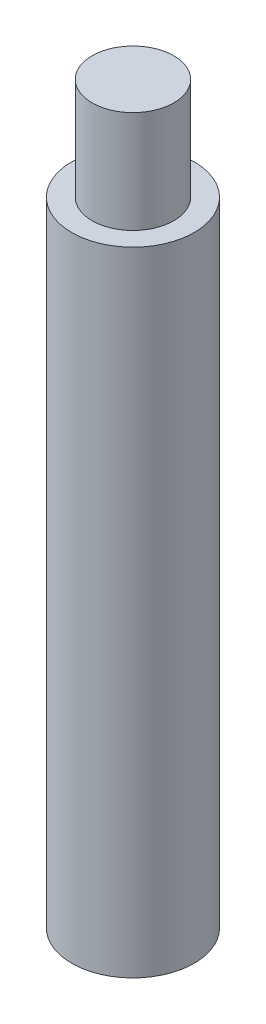
SolidWorks part; units mm, degrees
material "Plain Carbon Steel"
ref_plane "Front Plane" through (0, 0, 0) normal (0, 0, 1) x (1, 0, 0)
ref_plane "Top Plane" through (0, 0, 0) normal (0, 1, 0) x (1, 0, 0)
ref_plane "Right Plane" through (0, 0, 0) normal (1, 0, 0) x (0, 0, -1)
sketch "Sketch1" plane through (0, 0, 0) normal (0, 0, 1) x (1, 0, 0)
  line L0 (0, 0) -> (1.5, 0)
  line L1 (1.5, 0) -> (1.5, 15.5)
  line L2 (1.5, 15.5) -> (1, 15.5)
  line L3 (1, 15.5) -> (1, 18)
  line L4 (1, 18) -> (0, 18)
  line L5 (0, 18) -> (0, 0)
  dimension "D1" = 1.5
  dimension "D2" = 1
  dimension "D3" = 2.5
  dimension "D4" = 18
revolve "Revolve1" add sketch "Sketch1" angle 360 about L5
